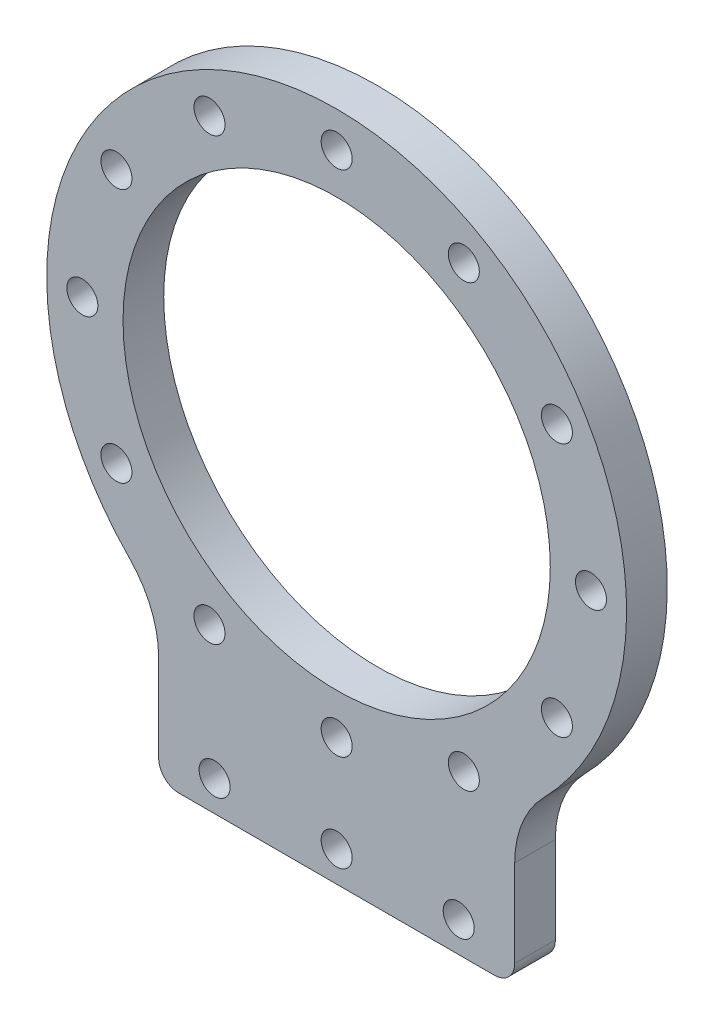
SolidWorks part; units mm, degrees
material "Thornel Mat VMA"
ref_plane "前视基准面" through (0, 0, 0) normal (0, 0, 1) x (1, 0, 0)
ref_plane "上视基准面" through (0, 0, 0) normal (0, 1, 0) x (1, 0, 0)
ref_plane "右视基准面" through (0, 0, 0) normal (1, 0, 0) x (0, 0, -1)
other "Configuration Table"
sketch "草图2" plane through (0, 0, 0) normal (0, 0, 1) x (1, 0, 0)
  line L1 (-17.5, -22.4944) -> (17.5, -22.4944)
  line L2 (-17.5, -22.4944) -> (-17.5, -37.5)
  line L3 (-17.5, -37.5) -> (17.5, -37.5)
  line L4 (17.5, -22.4944) -> (17.5, -37.5)
  line L5 (-17.5, -22.4944) -> (17.5, -37.5) construction
  line L6 (-17.5, -37.5) -> (17.5, -22.4944) construction
  circle A0 centre (0, 0) radius 28.5
  circle A1 centre (0, 0) radius 25 construction
  circle A2 centre (25, 0) radius 1.525
  circle A3 centre (21.6506, -12.5) radius 1.525
  circle A4 centre (12.5, -21.6506) radius 1.525
  circle A5 centre (0, -25) radius 1.525
  circle A6 centre (-12.5, -21.6506) radius 1.525
  circle A7 centre (-21.6506, -12.5) radius 1.525
  circle A8 centre (-25, 0) radius 1.525
  circle A9 centre (-21.6506, 12.5) radius 1.525
  circle A10 centre (-12.5, 21.6506) radius 1.525
  circle A11 centre (0, 25) radius 1.525
  circle A12 centre (12.5, 21.6506) radius 1.525
  circle A13 centre (21.6506, 12.5) radius 1.525
  point P7 (0, -29.9972)
  point P22 (0, 0)
  dimension "D1" = 57
  dimension "D2" = 50
  dimension "D3" = 3.05
  dimension "D5" = 35
  dimension "D6" = 37.5
  dimension "D4" = 12
extrude "凸台-拉伸1" add sketch "草图2" along normal blind 4 contours A4 L1 A0 A9 A8 A7 A6 A5 A3 A2 | A4 L1 A0 | A0 L2 L3 L4
sketch "草图4" plane through (0, 0, 4) normal (0, 0, 1) x (1, 0, 0)
  circle A0 centre (0, 0) radius 21
  dimension "D1" = 42
extrude "切除-拉伸1" cut sketch "草图4" against normal through all
sketch "草图5" plane through (0, 0, 4) normal (0, 0, 1) x (1, 0, 0)
  line L0 (-17.5, -34.5) -> (49982.5, -34.5) construction
  line L2 (-17.5, -37.5) -> (17.5, -37.5) construction
  line L3 (0, 0) -> (0, -34.5) construction
  circle A0 centre (0, -34.5) radius 1.525
  circle A1 centre (12, -34.5) radius 1.525
  circle A2 centre (-12, -34.5) radius 1.525
  dimension "D2" = 3.05
  dimension "D4" = 3.05
  dimension "D1" = 3
  dimension "D3" = 12
extrude "切除-拉伸2" cut sketch "草图5" against normal through all
fillet "圆角1" radius 2 2 edges at (17.5, -37.5, 2) (-17.5, -37.5, 2)
fillet "圆角2" radius 10 2 edges at (17.5, -22.4944, 2) (-17.5, -22.4944, 2)
